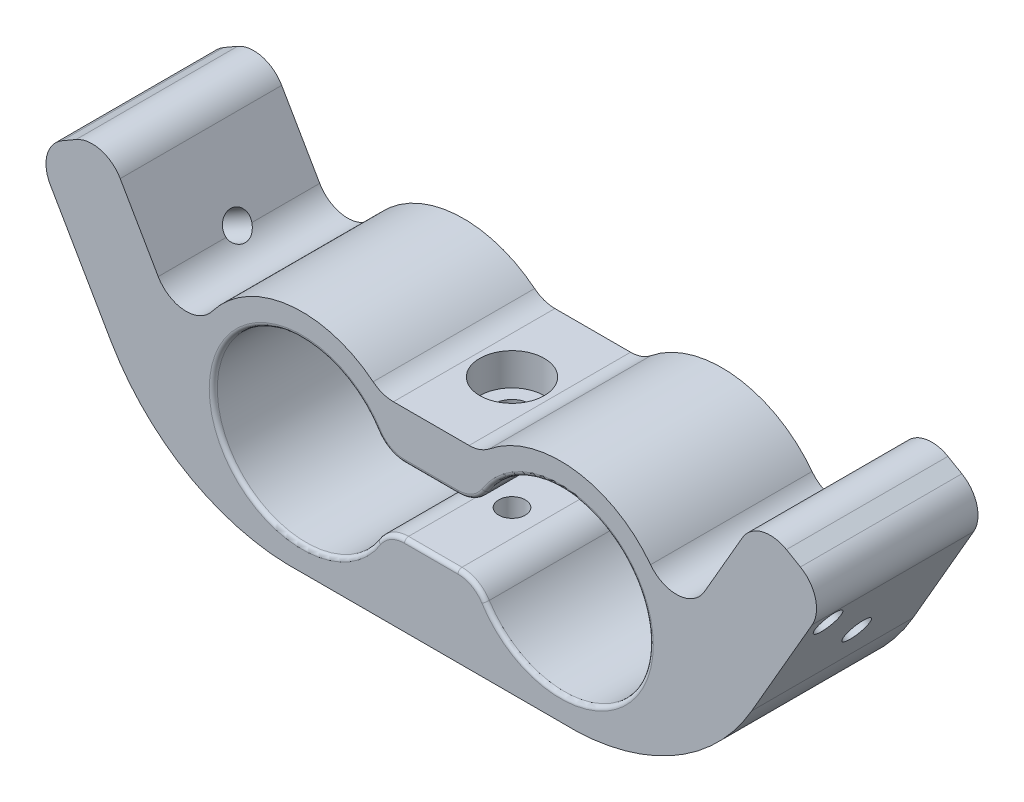
SolidWorks part; units mm, degrees
material "Сплав 2024"
ref_plane "Спереди" through (0, 0, 0) normal (0, 0, 1) x (1, 0, 0)
ref_plane "Сверху" through (0, 0, 0) normal (0, 1, 0) x (1, 0, 0)
ref_plane "Справа" through (0, 0, 0) normal (1, 0, 0) x (0, 0, -1)
sketch "Эскиз1" plane through (0, 0, 0) normal (0, 0, 1) x (1, 0, 0)
  line L0 (-97.2999, 0) -> (107.2229, 0) construction
  line L1 (0, 45.7486) -> (0, -47.2091) construction
  line L2 (-6.202, 10) -> (6.202, 10)
  line L3 (-5.753, 4) -> (5.753, 4)
  line L4 (43.1244, 18.9808) -> (28.1244, -7)
  line L5 (-43.1244, 18.9808) -> (-28.1244, -7)
  line L6 (-34.4641, 23.9808) -> (-26.1723, 9.619)
  line L7 (34.4641, 23.9808) -> (26.1723, 9.619)
  line L8 (-43.1244, 18.9808) -> (-34.4641, 23.9808)
  line L9 (34.4641, 23.9808) -> (43.1244, 18.9808)
  line L10 (-16, -14) -> (16, -14)
  line L11 (-5.753, -4) -> (5.753, -4)
  arc A0 (-5.753, 4) -> (-5.753, -4) centre (-16, 0) ccw
  arc A1 (5.753, -4) -> (5.753, 4) centre (16, 0) ccw
  arc A2 (-6.202, 10) -> (-26.1723, 9.619) centre (-16, 0) ccw
  arc A3 (-28.1244, -7) -> (-16, -14) centre (-16, 0) ccw
  arc A4 (16, -14) -> (28.1244, -7) centre (16, 0) ccw
  circle A5 centre (-16, 0) radius 14 construction
  arc A6 (26.1723, 9.619) -> (6.202, 10) centre (16, 0) ccw
  circle A7 centre (-16, 0) radius 11 construction
  point P8 (30, 0)
  point P10 (-5.4806, 3.2161)
  point P29 (-2, 0)
  point P36 (26.5194, 3.2161)
  dimension "D1" = 22
  dimension "D2" = 22
  dimension "D6" = 3
  dimension "D3" = 16
  dimension "D4" = 16
  dimension "D7" = 6
  dimension "D8" = 30
  dimension "D9" = 30
  dimension "D10" = 10
  dimension "D11" = 10
  dimension "D12" = 10
  dimension "D13" = 8
  dimension "D14" = 30
  dimension "D15" = 30
  dimension "D5" = 3
extrude "Бобышка-Вытянуть2" add sketch "Эскиз1" along normal blind 20
sketch "Эскиз3" plane through (0, 10, 0) normal (0, 1, 0) x (1, 0, 0)
  line L0 (0, 0) -> (0, -20) construction
  line L1 (6.202, -20) -> (-6.202, -20) construction
  line L2 (6.202, -10) -> (-6.202, -10) construction
  line L3 (6.202, -20) -> (6.202, 0) construction
  line L4 (-6.202, -20) -> (-6.202, 0) construction
hole_wizard "Цековка для винта с внутренним шестигранником M41" positions "Эскиз5" profile "Эскиз4" counterbore size "M4" standard "Ansi Metric" end condition up to next
sketch "Эскиз5" plane through (0, 10, 0) normal (0, 1, 0) x (1, 0, 0)
  line L0 (0, 0) -> (0, -20) construction
  point P0 (0, -10)
sketch "Эскиз4" plane through (0, 10, 10) normal (1, 0, 0) x (0, 0, 1)
  line L0 (0, 0) -> (0, 6)
  line L1 (0, 6) -> (2.25, 6)
  line L3 (2.25, 6) -> (2.25, 4)
  line L4 (2.25, 4) -> (4, 4)
  line L5 (4, 4) -> (4, 0)
  line L7 (4, 0) -> (0, 0)
  line L11 (0, -6.35) -> (0, 107.95) construction
  dimension "Диаметр сквозного отверстия" = 4.5
  dimension "Глубина сквозного отверстия" = 6
  dimension "Диаметр цековки" = 8
  dimension "Глубина цековки" = 4
hole_wizard "Отверстие обработанное метчиком M4x0.71" positions "Эскиз7" profile "Эскиз6" tap size "M4x0.7" standard "Ansi Metric" end condition through all
sketch "Эскиз7" plane through (0, -4, 0) normal (0, 1, 0) x (1, 0, 0)
  line L0 (0, 0) -> (0, -20) construction
  point P0 (0, -10)
sketch "Эскиз6" plane through (0, -4, 10) normal (1, 0, 0) x (0, 0, 1)
  line L0 (0, 0) -> (0, 10)
  line L1 (0, 10) -> (1.65, 10)
  line L2 (1.65, 10) -> (1.65, 0)
  line L5 (1.65, 0) -> (0, 0)
  line L11 (0, -6.35) -> (0, 107.95) construction
  dimension "Диаметр проходного сверла" = 3.3
  dimension "Глубина проходного сверла" = 10
cosmetic thread "Отверстие резьбы1" parameters "D2"=4
sketch "Эскиз15" plane through (0, 0, 20) normal (0, 0, 1) x (1, 0, 0)
  line L0 (0, 10) -> (0, -14) construction
  line L1 (6.202, 10) -> (-6.202, 10) construction
  line L2 (-16, -14) -> (16, -14) construction
  line L3 (43.1244, 18.9808) -> (49.1865, 15.4808)
  line L4 (49.1865, 15.4808) -> (39.6797, -0.9856)
  line L5 (43.1244, 18.9808) -> (34.4641, 23.9808) construction
  line L6 (28.1244, -7) -> (43.1244, 18.9808) construction
  line L7 (28.1244, -7) -> (43.1244, 18.9808)
  line L8 (-49.1865, 15.4808) -> (-39.6797, -0.9856)
  line L9 (-28.1244, -7) -> (-43.1244, 18.9808)
  line L10 (-43.1244, 18.9808) -> (-49.1865, 15.4808)
  arc A0 (39.6797, -0.9856) -> (16, -14) centre (17.098, 12.0519) cw
  arc A1 (16, -14) -> (28.1244, -7) centre (16, 0) ccw construction
  arc A2 (16, -14) -> (28.1244, -7) centre (16, 0) ccw
  arc A3 (-39.6797, -0.9856) -> (-16, -14) centre (-17.098, 12.0519) ccw
  arc A4 (-16, -14) -> (-28.1244, -7) centre (-16, 0) cw
  dimension "D1" = 7
extrude "Бобышка-Вытянуть4" add sketch "Эскиз15" against normal up to surface (20 mm away) up to face at (0, 7.3573, 0)
sketch "Эскиз16" plane through (0, 0, 20) normal (0, 0, 1) x (1, 0, 0)
  line L0 (40.5263, 20.4808) -> (29.8564, 2)
  line L1 (49.1865, 15.4808) -> (34.4641, 23.9808) construction
  line L2 (39.6797, -0.9856) -> (49.1865, 15.4808) construction
  line L3 (40.5263, 20.4808) -> (34.4641, 23.9808)
  line L4 (34.4641, 23.9808) -> (26.1723, 9.619)
  line L5 (0, 10) -> (0, -14) construction
  line L6 (6.202, 10) -> (-6.202, 10) construction
  line L7 (-16, -14) -> (16, -14) construction
  line L8 (-40.5263, 20.4808) -> (-34.4641, 23.9808)
  line L9 (-34.4641, 23.9808) -> (-26.1723, 9.619)
  line L10 (-40.5263, 20.4808) -> (-29.8564, 2)
  arc A0 (26.1723, 9.619) -> (29.8564, 2) centre (16, 0) cw
  arc A1 (-26.1723, 9.619) -> (-29.8564, 2) centre (-16, 0) ccw
  dimension "D1" = 10
extrude "Вырез-Вытянуть1" cut sketch "Эскиз16" against normal through all
fillet "Скругление1" radius 4 12 edges at (-5.753, -4, 10) (5.753, -4, 10) (5.753, 4, 10) (-5.753, 4, 10) (6.202, 10, 10) (-6.202, 10, 10) (49.1865, 15.4808, 10) (40.5263, 20.4808, 10) (29.8564, 2, 10) (-49.1865, 15.4808, 10) (-40.5263, 20.4808, 10) (-29.8564, 2, 10)
sketch "Эскиз8" plane through (30.1865, -17.4282, 0) normal (0.866, -0.5, 0) x (0, 0, -1)
  line L0 (-10, 34) -> (-10, 8) construction
  line L3 (-20, 25) -> (0, 25) construction
  line L7 (-20, 38) -> (0, 38) construction
  line L8 (0, 34) -> (-20, 34) construction
  line L9 (-20, 18.9862) -> (-20, 34) construction
  line L10 (0, 34) -> (0, 18.9862) construction
  dimension "D1" = 13
hole_wizard "Отверстие обработанное метчиком M4x0.72" positions "Эскиз10" profile "Эскиз9" tap size "M4x0.7" standard "Ansi Metric" end condition through all
sketch "Эскиз10" plane through (31.1108, -15.8274, 5.4333) normal (0.866, -0.5, 0) x (-0.5, -0.866, 0)
  line L0 (-23.1515, -14.5667) -> (-23.1515, 5.4333) construction
  point P0 (-23.1515, -4.5667)
sketch "Эскиз9" plane through (42.6865, 4.2224, 10) normal (0, 0, 1) x (0.5, 0.866, 0)
  line L0 (0, 0) -> (0, 85.6936)
  line L1 (0, 85.6936) -> (1.65, 85.6936)
  line L2 (1.65, 85.6936) -> (1.65, 0)
  line L5 (1.65, 0) -> (0, 0)
  line L11 (0, -6.35) -> (0, 107.95) construction
  dimension "Диаметр проходного сверла" = 3.3
  dimension "Глубина проходного сверла" = 85.6936
cosmetic thread "Отверстие резьбы4" parameters "D2"=4
ref_plane "Плоскость1" through (0, 0, 0) normal (-1, 0, 0) x (0, 0, 1)
mirror "Зеркальное отражение1" about plane through (0, 0, 0) normal (-1, 0, 0) of "Отверстие обработанное метчиком M4x0.72"
sketch "Эскиз11" [suppressed] plane through (-17.8995, -17.8995, 0) normal (-0.7071, -0.7071, 0) x (0, 0, 1)
  line L0 (10, 28.3137) -> (22.9622, 41.2759) construction
  line L1 (19.5, 11.3137) -> (19.5, 42.3137) construction
  circle A0 centre (17.0711, 35.3848) radius 2
  dimension "D2" = 4
  dimension "D1" = 45
  dimension "D3" = 10
extrude "Бобышка-Вытянуть3" [suppressed] add sketch "Эскиз11" along normal blind 8
mirror "Зеркальное отражение2" [suppressed] about plane through (0, 0, 0) normal (-1, 0, 0)
sketch "Эскиз12" plane through (-30.1865, -17.4282, 0) normal (-0.866, -0.5, 0) x (0, 0, 1)
  line L0 (10, 25) -> (28.4708, 43.4708) construction
  line L2 (20, 34) -> (20, 18.9862) construction
  point P5 (17.0711, 32.0711)
  dimension "D1" = 45
  dimension "D2" = 10
hole_wizard "Отверстие обработанное метчиком M4x0.73" positions "Эскиз14" profile "Эскиз13" tap size "M4x0.7" standard "Ansi Metric"
sketch "Эскиз14" plane through (-31.5395, -15.0848, -4.7261) normal (-0.866, -0.5, 0) x (-0.5, 0.866, 0)
  point P0 (29.3651, -21.7972)
sketch "Эскиз13" plane through (-46.2221, 10.3462, 17.0711) normal (0, 0, 1) x (0.5, -0.866, 0)
  line L0 (0, 0) -> (0, 4.9914)
  line L1 (0, 4.9914) -> (1.65, 4)
  line L2 (1.65, 4) -> (1.65, 0)
  line L5 (1.65, 0) -> (0, 0)
  line L10 (0, 4.9914) -> (-1.65, 4) construction
  line L11 (0, -6.35) -> (0, 107.95) construction
  dimension "Диаметр сверла" = 3.3
  dimension "Глубина сверла" = 4
  dimension "Угол заточки сверла" = 118
cosmetic thread "Отверстие резьбы3" parameters "D1"=6, "D2"=4
mirror "Зеркальное отражение3" about plane through (0, 0, 0) normal (-1, 0, 0) of "Отверстие обработанное метчиком M4x0.73"
fillet "Скругление6" radius 0.5 16 edges at (-5.2436, 4.4976, 0) (0, 4, 0) (5.2436, 4.4976, 0) (27, 0, 0) (5.2436, -4.4976, 0) (0, -4, 0) (-5.2436, -4.4976, 0) (-5.2436, 4.4976, 20) (0, 4, 20) (5.2436, 4.4976, 20) (27, 0, 20) (5.2436, -4.4976, 20) (0, -4, 20) (-5.2436, -4.4976, 20) (-27, 0, 0) (-27, 0, 20)
equation "\"D2@Эскиз1\"=\"D1@Эскиз1\""
equation "\"D4@Эскиз1\"=\"D3@Эскиз1\""
